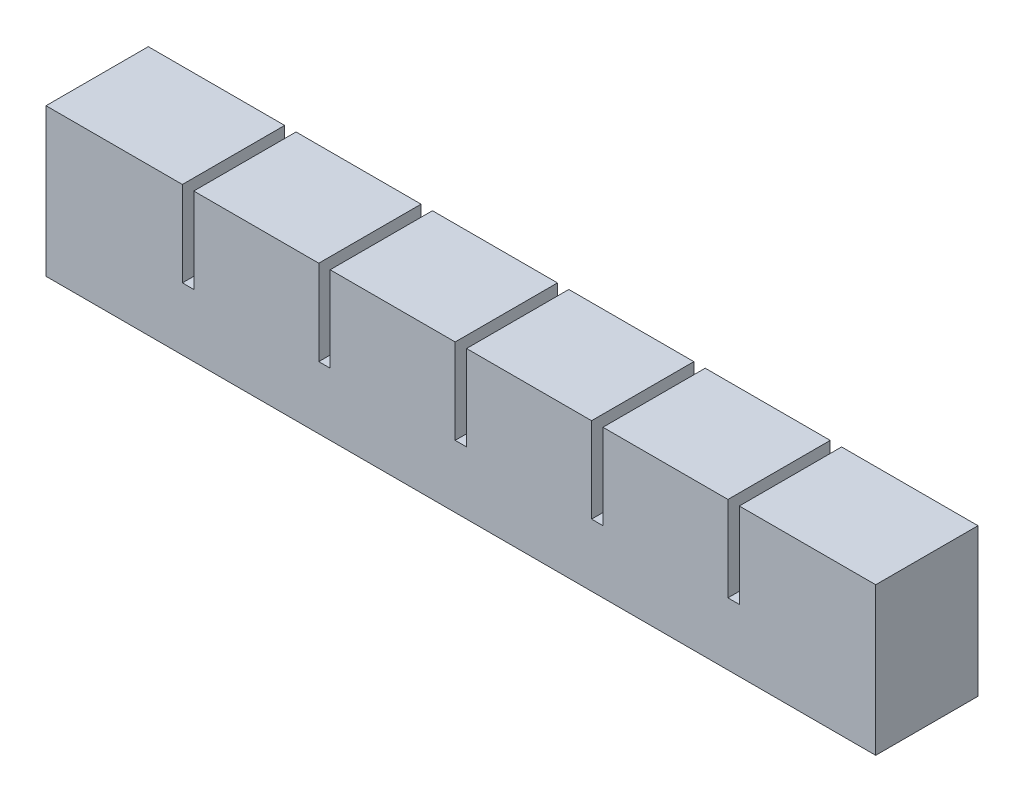
SolidWorks part; units mm, degrees
ref_plane "Front Plane" through (0, 0, 0) normal (0, 0, 1) x (1, 0, 0)
ref_plane "Top Plane" through (0, 0, 0) normal (0, 1, 0) x (1, 0, 0)
ref_plane "Right Plane" through (0, 0, 0) normal (1, 0, 0) x (0, 0, -1)
sketch "Sketch1" plane through (0, 0, 0) normal (0, 0, 1) x (1, 0, 0)
  line L1 (0, 0) -> (22, 0)
  line L2 (0, 0) -> (0, 20)
  line L3 (0, 20) -> (22, 20)
  line L4 (22, 0) -> (22, 20)
  dimension "D1" = 22
  dimension "D2" = 20
extrude "Boss-Extrude1" add sketch "Sketch1" along normal blind 18
sketch "Sketch2" plane through (0, 0, 0) normal (0, -1, 0) x (1, 0, 0)
  line L0 (22, 18) -> (22, 0) construction
  line L1 (5, 13) -> (17, 13)
  line L2 (5, 13) -> (5, 5)
  line L3 (5, 5) -> (17, 5)
  line L4 (17, 13) -> (17, 5)
  line L5 (0, 18) -> (22, 18) construction
  line L6 (0, 18) -> (0, 0) construction
  line L7 (0, 0) -> (22, 0) construction
  dimension "D1" = 5
  dimension "D2" = 5
  dimension "D3" = 5
  dimension "D4" = 5
extrude "Cut-Extrude1" cut sketch "Sketch2" against normal blind 15
sketch "Sketch3" plane through (22, 0, 0) normal (1, 0, 0) x (0, 0, -1)
  line L0 (0, 0) -> (0, 20) construction
  line L1 (-18, 0) -> (0, 0)
  line L2 (-18, 0) -> (-18, 5)
  line L3 (-18, 5) -> (0, 5)
  line L4 (0, 0) -> (0, 5)
  dimension "D1" = 5
extrude "Boss-Extrude2" add sketch "Sketch3" along normal blind 2
pattern_linear "LPattern1" count 6 spacing 24 along (1, 0, 0) of bodies 103
combine bodies "Combine1" operation type add bodies to combine 105 103 106 107 108 104
sketch "Sketch4" plane through (142, 0, 0) normal (1, 0, 0) x (0, 0, -1)
  line L1 (-18, 20) -> (0, 20)
  line L2 (-18, 20) -> (-18, 5)
  line L3 (-18, 5) -> (0, 5)
  line L4 (0, 20) -> (0, 5)
extrude "Boss-Extrude3" add sketch "Sketch4" along normal up to surface (2 mm away) up to face at (144, 2.5, 9)
sketch "Sketch5" plane through (0, 0, 0) normal (-1, 0, 0) x (0, 0, 1)
  line L1 (0, 20) -> (18, 20)
  line L2 (0, 20) -> (0, 0)
  line L3 (0, 0) -> (18, 0)
  line L4 (18, 20) -> (18, 0)
extrude "Boss-Extrude4" add sketch "Sketch5" along normal blind 2
ref_point "Point1"
sketch "Sketch6" plane through (0, 0, 0) normal (0, -1, 0) x (-1, 0, 0)
  line L0 (-137, -5) -> (-137, -13) construction
  line L1 (-5, -8) -> (-137, -8)
  line L2 (-5, -8) -> (-5, -10)
  line L3 (-5, -10) -> (-137, -10)
  line L4 (-137, -8) -> (-137, -10)
  line L5 (-5, -8) -> (-137, -10) construction
  line L6 (-5, -10) -> (-137, -8) construction
  point P0 (-71, -9)
  dimension "D1" = 2
extrude "Cut-Extrude2" cut sketch "Sketch6" against normal blind 2
sketch "Sketch7" plane through (0, 0, 0) normal (0, -1, 0) x (1, 0, 0)
  line L1 (-2, 18) -> (144, 18)
  line L2 (-2, 18) -> (-2, 0)
  line L3 (-2, 0) -> (144, 0)
  line L4 (144, 18) -> (144, 0)
extrude "Boss-Extrude5" add sketch "Sketch7" along normal blind 6
